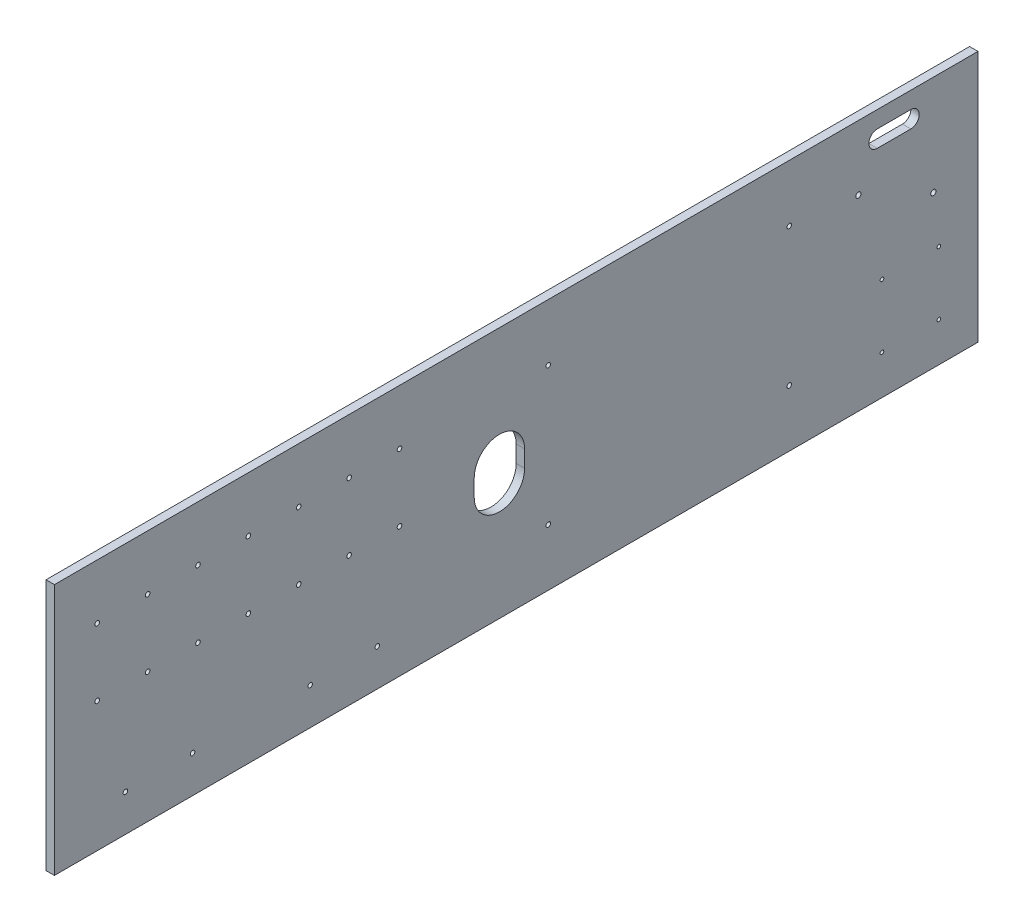
SolidWorks part; units mm, degrees
material "Acrylic (Medium-high impact)"
ref_plane "Front Plane" through (0, 0, 0) normal (0, 0, 1) x (1, 0, 0)
ref_plane "Top Plane" through (0, 0, 0) normal (0, 1, 0) x (1, 0, 0)
ref_plane "Right Plane" through (0, 0, 0) normal (1, 0, 0) x (0, 0, -1)
sketch "Sketch1" plane through (0, 0, 0) normal (1, 0, 0) x (0, 0, -1)
  line L0 (146.05, 95.25) -> (158.75, 95.25)
  line L1 (146.05, -95.25) -> (-146.05, -95.25)
  line L2 (146.05, -95.25) -> (146.05, 95.25) construction
  line L3 (146.05, 95.25) -> (-146.05, 95.25)
  line L4 (-146.05, -95.25) -> (-146.05, 95.25)
  line L5 (146.05, -95.25) -> (-146.05, 95.25) construction
  line L6 (146.05, 95.25) -> (-146.05, -95.25) construction
  line L7 (552.45, -95.25) -> (158.75, -95.25)
  line L8 (552.45, -95.25) -> (552.45, 95.25)
  line L9 (552.45, 95.25) -> (158.75, 95.25)
  line L10 (158.75, -95.25) -> (158.75, 95.25) construction
  line L11 (552.45, -95.25) -> (158.75, 95.25) construction
  line L12 (552.45, 95.25) -> (158.75, -95.25) construction
  line L13 (158.75, -95.25) -> (146.05, -95.25)
  point P0 (0, 0)
  point P6 (355.6, 0)
  dimension "D1" = 292.1
  dimension "D2" = 190.5
  dimension "D3" = 12.7
  dimension "D4" = 393.7
extrude "Boss-Extrude1" add sketch "Sketch1" along normal blind 6.35
sketch "Sketch2" plane through (0, 0, 0) normal (-1, 0, 0) x (0, 0, 1)
  line L0 (-552.45, -95.25) -> (-552.45, 95.25) construction
  line L1 (-501.65, 76.2) -> (-476.25, 76.2) construction
  line L2 (-501.65, 82.55) -> (-476.25, 82.55)
  line L3 (-501.65, 69.85) -> (-476.25, 69.85)
  line L4 (-552.45, 95.25) -> (146.05, 95.25) construction
  line L5 (-190.5, 6.35) -> (-190.5, -6.35) construction
  line L6 (-171.45, 6.35) -> (-171.45, -6.35)
  line L7 (-209.55, 6.35) -> (-209.55, -6.35)
  line L9 (146.05, 95.25) -> (146.05, -95.25) construction
  circle A0 centre (-518.668, 19.685) radius 3.302 construction
  arc A1 (-171.45, 6.35) -> (-209.55, 6.35) centre (-190.5, 6.35) ccw
  circle A2 centre (-114.9393, 2.9132) radius 2.2479 construction
  circle A3 centre (-76.8393, 2.9132) radius 2.2479 construction
  circle A4 centre (-38.7393, 2.9132) radius 2.2479 construction
  circle A5 centre (-0.6393, 2.9132) radius 2.2479 construction
  circle A6 centre (37.4607, 2.9132) radius 2.2479 construction
  circle A7 centre (75.5607, 2.9132) radius 2.2479 construction
  circle A8 centre (113.6607, 2.9132) radius 2.2479 construction
  circle A9 centre (113.6607, 53.7132) radius 2.2479 construction
  circle A10 centre (75.5607, 53.7132) radius 2.2479 construction
  circle A11 centre (37.4607, 53.7132) radius 2.2479 construction
  circle A12 centre (-0.6393, 53.7132) radius 2.2479 construction
  circle A13 centre (-38.7393, 53.7132) radius 2.2479 construction
  circle A14 centre (-76.8393, 53.7132) radius 2.2479 construction
  circle A15 centre (-114.9393, 53.7132) radius 2.2479 construction
  circle A16 centre (-114.9393, 2.9132) radius 2.2479 construction
  circle A17 centre (-76.8393, 2.9132) radius 2.2479 construction
  circle A18 centre (-38.7393, 2.9132) radius 2.2479 construction
  circle A19 centre (-0.6393, 2.9132) radius 2.2479 construction
  circle A20 centre (37.4607, 2.9132) radius 2.2479 construction
  circle A21 centre (75.5607, 2.9132) radius 2.2479 construction
  circle A22 centre (113.6607, 2.9132) radius 2.2479 construction
  circle A23 centre (113.6607, 53.7132) radius 2.2479 construction
  circle A24 centre (75.5607, 53.7132) radius 2.2479 construction
  circle A25 centre (37.4607, 53.7132) radius 2.2479 construction
  circle A26 centre (-0.6393, 53.7132) radius 2.2479 construction
  circle A27 centre (-38.7393, 53.7132) radius 2.2479 construction
  circle A28 centre (-76.8393, 53.7132) radius 2.2479 construction
  circle A29 centre (-114.9393, 53.7132) radius 2.2479 construction
  circle A30 centre (92.3368, -67.3143) radius 2.2479 construction
  circle A31 centre (41.5368, -67.3143) radius 2.2479 construction
  circle A32 centre (-47.3632, -67.3143) radius 2.2479 construction
  circle A33 centre (-98.1632, -67.3143) radius 2.2479 construction
  circle A34 centre (92.3368, -67.3143) radius 2.2479 construction
  circle A35 centre (41.5368, -67.3143) radius 2.2479 construction
  circle A36 centre (-47.3632, -67.3143) radius 2.2479 construction
  circle A37 centre (-98.1632, -67.3143) radius 2.2479 construction
  circle A38 centre (-479.806, -17.78) radius 1.905 construction
  circle A39 centre (-522.859, -17.7824) radius 1.905 construction
  circle A40 centre (-522.859, -65.532) radius 1.905 construction
  circle A41 centre (-479.806, -65.532) radius 1.905 construction
  circle A42 centre (-479.806, -17.78) radius 1.905 construction
  circle A43 centre (-522.859, -17.7824) radius 1.905 construction
  circle A44 centre (-522.859, -65.532) radius 1.905 construction
  circle A45 centre (-479.806, -65.532) radius 1.905 construction
  circle A46 centre (-409.7229, -52.197) radius 2.667 construction
  circle A47 centre (-409.7229, 52.197) radius 2.667 construction
  circle A48 centre (-227.4525, 52.197) radius 2.667 construction
  circle A49 centre (-227.4525, -52.197) radius 2.667 construction
  circle A50 centre (-409.7229, -52.197) radius 2.667 construction
  circle A51 centre (-409.7229, 52.197) radius 2.667 construction
  circle A52 centre (-227.4525, 52.197) radius 2.667 construction
  circle A53 centre (-227.4525, -52.197) radius 2.667 construction
  circle A54 centre (-462.026, 46.355) radius 3.302 construction
  arc A55 (-501.65, 82.55) -> (-501.65, 69.85) centre (-501.65, 76.2) ccw
  circle A56 centre (-518.668, 19.685) radius 3.302 construction
  arc A57 (-476.25, 69.85) -> (-476.25, 82.55) centre (-476.25, 76.2) ccw
  circle A58 centre (-462.026, 46.355) radius 3.302 construction
  arc A59 (-209.55, -6.35) -> (-171.45, -6.35) centre (-190.5, -6.35) ccw
  circle A60 centre (113.6607, 53.7132) radius 1.7272
  circle A61 centre (75.5607, 53.7132) radius 1.7272
  circle A62 centre (37.4607, 53.7132) radius 1.7272
  circle A63 centre (-0.6393, 53.7132) radius 1.7272
  circle A64 centre (-38.7393, 53.7132) radius 1.7272
  circle A65 centre (-76.8393, 53.7132) radius 1.7272
  circle A66 centre (-114.9393, 53.7132) radius 1.7272
  circle A67 centre (-114.9393, 2.9132) radius 1.7272
  circle A68 centre (-76.8393, 2.9132) radius 1.7272
  circle A69 centre (-38.7393, 2.9132) radius 1.7272
  circle A70 centre (-0.6393, 2.9132) radius 1.7272
  circle A71 centre (37.4607, 2.9132) radius 1.7272
  circle A72 centre (75.5607, 2.9132) radius 1.7272
  circle A73 centre (113.6607, 2.9132) radius 1.7272
  circle A74 centre (92.3368, -67.3143) radius 1.7272
  circle A75 centre (41.5368, -67.3143) radius 1.7272
  circle A76 centre (-47.3632, -67.3143) radius 1.7272
  circle A77 centre (-98.1632, -67.3143) radius 1.7272
  circle A78 centre (-227.4525, 52.197) radius 1.7272
  circle A79 centre (-227.4525, -52.197) radius 1.7272
  circle A80 centre (-409.7229, -52.197) radius 1.7272
  circle A81 centre (-409.7229, 52.197) radius 1.7272
  circle A82 centre (-522.859, -17.7824) radius 1.3891
  circle A83 centre (-479.806, -17.78) radius 1.3891
  circle A84 centre (-479.806, -65.532) radius 1.3891
  circle A85 centre (-522.859, -65.532) radius 1.3891
  circle A86 centre (-462.026, 46.355) radius 1.9844
  circle A87 centre (-518.668, 19.685) radius 1.9844
  point P85 (-190.5, 0)
  point P90 (-488.95, 76.2)
  point P96 (-518.668, 46.355)
  dimension "D2" = 38.1
  dimension "D1" = 12.7
  dimension "D8" = 3.4544
  dimension "D9" = 2.7781
  dimension "D10" = 3.9688
  dimension "D4" = 25.4
  dimension "D5" = 50.8
  dimension "D3" = 12.7
  dimension "D6" = 12.7
  dimension "D7" = 317.5
extrude "Cut-Extrude1" cut sketch "Sketch2" against normal through all
sketch "Sketch3" [suppressed] plane through (0, 0, 0) normal (-1, 0, 0) x (0, 0, 1)
  circle A0 centre (-403.6403, 30.1821) radius 17.0258
  circle A1 centre (56.8306, -25.5387) radius 44.024
extrude "Cut-Extrude2" [suppressed] cut sketch "Sketch3" against normal through all
sketch "Sketch4" plane through (6.35, 0, 0) normal (1, 0, 0) x (0, 0, -1)
  line L0 (552.45, -95.25) -> (552.45, 95.25) construction
  line L1 (-146.05, -95.25) -> (552.45, -95.25) construction
  line L2 (397.51, -57.15) -> (397.51, -95.25)
  line L3 (397.51, -95.25) -> (427.99, -95.25)
  line L5 (427.99, -95.25) -> (427.99, -57.15)
  circle A0 centre (-99.7543, -63.5) radius 1.0795 construction
  circle A1 centre (1.8457, -63.5) radius 1.0795 construction
  circle A2 centre (54.2357, 17.0307) radius 1.8387 construction
  circle A3 centre (115.2719, 17.0307) radius 1.8387 construction
  circle A4 centre (54.2357, 65.8749) radius 1.8387 construction
  circle A5 centre (115.2719, 65.8749) radius 1.8387 construction
  circle A6 centre (54.2357, 17.0307) radius 1.8387
  circle A7 centre (115.2719, 17.0307) radius 1.8387
  circle A8 centre (54.2357, 65.8749) radius 1.8387
  circle A9 centre (115.2719, 65.8749) radius 1.8387
  circle A10 centre (-99.7543, 63.5) radius 1.0795 construction
  circle A11 centre (1.8457, 63.5) radius 1.0795 construction
  circle A12 centre (-99.7543, -63.5) radius 1.0795
  circle A13 centre (1.8457, -63.5) radius 1.0795
  circle A14 centre (-99.7543, 63.5) radius 1.0795
  circle A15 centre (1.8457, 63.5) radius 1.0795
  circle A16 centre (476.25, -57.15) radius 11.1125
  circle A17 centre (476.25, -57.15) radius 20.955 construction
  arc A18 (427.99, -57.15) -> (397.51, -57.15) centre (412.75, -57.15) ccw
  circle A19 centre (349.25, -57.15) radius 11.1125
  circle A20 centre (222.25, -50.8) radius 22.225
  circle A21 centre (285.75, -57.15) radius 11.1125
  dimension "D1" = 22.225
  dimension "D4" = 41.91
  dimension "D5" = 30.48
  dimension "D8" = 44.45
  dimension "D2" = 76.2
  dimension "D3" = 38.1
  dimension "D6" = 63.5
  dimension "D7" = 63.5
  dimension "D9" = 44.45
  dimension "D10" = 127
  dimension "D11" = 63.5
extrude "Cut-Extrude3" [suppressed] cut sketch "Sketch4" against normal through all
